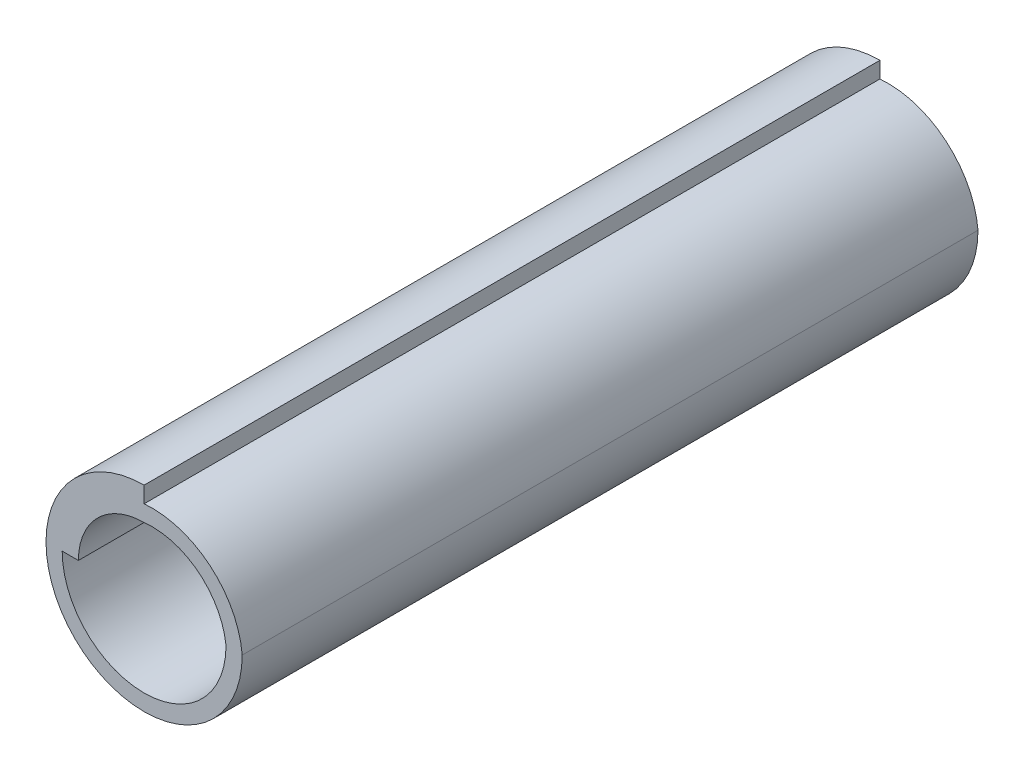
SolidWorks part; units mm, degrees
ref_plane "Plane1" through (0, 0, 0) normal (0, 0, 1) x (1, 0, 0)
ref_plane "Plane2" through (0, 0, 0) normal (0, 1, 0) x (1, 0, 0)
ref_plane "Plane3" through (0, 0, 0) normal (1, 0, 0) x (0, 0, -1)
other "Configuration Table"
sketch "Sketch1" plane through (0, 0, 0) normal (0, 0, 1) x (1, 0, 0)
  line L0 (0, 1.67) -> (0, 2)
  line L1 (-1.67, 0) -> (-1.34, 0)
  line L2 (0, 1.34) -> (1.67, 0) construction
  line L3 (0.165, -0.165) -> (0.835, 0.67) construction
  line L4 (0, 1.67) -> (2, 0) construction
  line L5 (0.165, -0.165) -> (1, 0.835) construction
  arc A0 (0, 2) -> (2, 0) centre (0, 0) ccw
  arc A1 (-1.67, 0) -> (1.67, 0) centre (0, 0) ccw
  arc A2 (0, 1.34) -> (-1.34, 0) centre (0, 0) ccw
  arc A3 (1.67, 0) -> (0, 1.34) centre (0.165, -0.165) ccw
  arc A4 (2, 0) -> (0, 1.67) centre (0.165, -0.165) ccw
  dimension "Diameter" = 4
  dimension "D2" = 3.34
  dimension "Thickness" = 0.33
  dimension "D1" = 0.33
extrude "Base-Extrude" add sketch "Sketch1" along normal mid plane 15
equation "\"D1@Sketch1\" = \"Thickness@Sketch1\""
equation "\"D2@Sketch1\" = \"Diameter@Sketch1\" - \"Thickness@Sketch1\" * 2"
